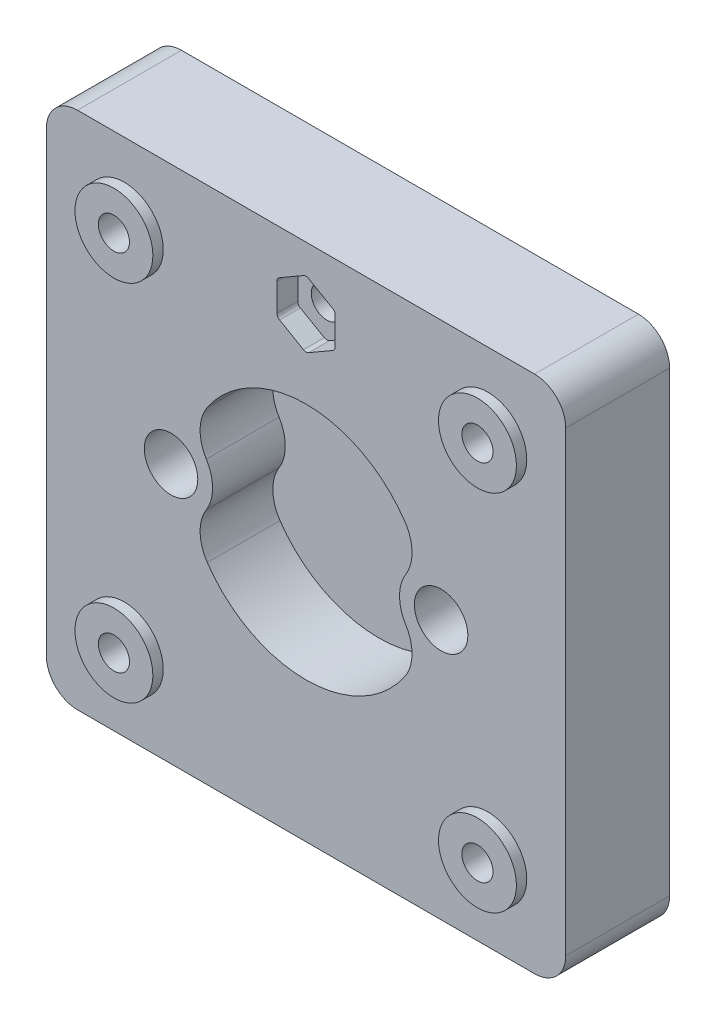
SolidWorks part; units mm, degrees
other "Cathode"
ref_plane "Front Plane" through (0, 0, 0) normal (0, 0, 1) x (1, 0, 0)
ref_plane "Top Plane" through (0, 0, 0) normal (0, 1, 0) x (1, 0, 0)
ref_plane "Right Plane" through (0, 0, 0) normal (1, 0, 0) x (0, 0, -1)
sketch "Sketch1" plane through (0, 0, 0) normal (0, 1, 0) x (1, 0, 0)
  line L1 (25, -25) -> (-25, -25)
  line L2 (25, -25) -> (25, 25)
  line L3 (25, 25) -> (-25, 25)
  line L4 (-25, -25) -> (-25, 25)
  line L5 (25, -25) -> (-25, 25) construction
  line L6 (25, 25) -> (-25, -25) construction
  point P0 (0, 0)
  dimension "D1" = 50
  dimension "D2" = 50
extrude "Body" add sketch "Sketch1" along normal blind 10
sketch "Sketch2" plane through (0, 10, 0) normal (0, 1, 0) x (1, 0, 0)
  circle A0 centre (0, 0) radius 11.5
  dimension "D1" = 23
extrude "Cut view" cut sketch "Sketch2" against normal blind 7
fillet "FilletBody" radius 3 4 edges at (-25, 5, -25) (25, 5, -25) (25, 5, 25) (-25, 5, 25)
sketch "Sketch3" plane through (0, 10, 0) normal (0, 1, 0) x (1, 0, 0)
  line L0 (-25, 22) -> (-25, -22) construction
  line L1 (22, 25) -> (-22, 25) construction
  line L2 (-38.934, 0) -> (38.0552, 0) construction
  line L3 (0, 29.5616) -> (0, -31.3312) construction
  circle A0 centre (-17.5, 17.5) radius 3.75
  circle A1 centre (17.5, 17.5) radius 3.75
  circle A2 centre (17.5, -17.5) radius 3.75
  circle A3 centre (-17.5, -17.5) radius 3.75
  dimension "D1" = 7.5
  dimension "D2" = 7.5
  dimension "D3" = 7.5
extrude "Bolt extrude" add sketch "Sketch3" along normal blind 1
sketch "Sketch4" plane through (0, 11, 0) normal (0, 1, 0) x (1, 0, 0)
  line L2 (-40.7589, 0) -> (37.9331, 0) construction
  line L3 (-5.5, 0) -> (5.5, 0) construction
  line L4 (0, 29.2624) -> (0, -30.4072) construction
  circle A0 centre (-17.5, 17.5) radius 1.5
  circle A1 centre (17.5, 17.5) radius 1.5
  circle A2 centre (17.5, -17.5) radius 1.5
  circle A3 centre (-17.5, -17.5) radius 1.5
  dimension "D1" = 3
extrude "Bolt" cut sketch "Sketch4" against normal blind 16 and the other way blind 10
sketch "Sketch5" plane through (0, 10, 0) normal (0, 1, 0) x (1, 0, 0)
  line L0 (22, 25) -> (-22, 25) construction
  line L1 (0, 22.2332) -> (-2.8, 20.6166)
  line L2 (-2.8, 20.6166) -> (-2.8, 17.3834)
  line L3 (-2.8, 17.3834) -> (0, 15.7668)
  line L4 (0, 15.7668) -> (2.8, 17.3834)
  line L5 (2.8, 17.3834) -> (2.8, 20.6166)
  line L6 (2.8, 20.6166) -> (0, 22.2332)
  circle A0 centre (0, 19) radius 2.8 construction
  dimension "D2" = 5.6
  dimension "D1" = 6
extrude "Hex" cut sketch "Sketch5" against normal blind 2
sketch "Sketch19" plane through (0, 8, 0) normal (0, 1, 0) x (1, 0, 0)
  circle A0 centre (0, 19) radius 1.5
  dimension "D1" = 3
extrude "Hex_bolt" cut sketch "Sketch19" against normal blind 3
sketch "Sketch6" plane through (0, 10, 0) normal (0, 1, 0) x (1, 0, 0)
  line L0 (-5.5, 0) -> (5.5, 0) construction
  line L1 (-25, 22) -> (-25, -22) construction
  line L2 (0, 27.3129) -> (0, -30.0369) construction
  circle A0 centre (-13, 0) radius 4
  circle A1 centre (13, 0) radius 4
  dimension "D2" = 8
  dimension "D1" = 12
extrude "Field1" add sketch "Sketch6" against normal blind 7
fillet "Field2" radius 4 4 edges at (10.9712, 6.5, -3.4473) (10.9712, 6.5, 3.4473) (-10.9712, 6.5, 3.4473) (-10.9712, 6.5, -3.4473)
sketch "Sketch7" plane through (0, 10, 0) normal (0, 1, 0) x (1, 0, 0)
  line L0 (-5.5, 0) -> (5.5, 0) construction
  line L1 (-25, 22) -> (-25, -22) construction
  line L2 (0, 27.9755) -> (0, -30.6258) construction
  circle A0 centre (-13, 0) radius 2.575
  circle A1 centre (13, 0) radius 2.575
  dimension "D2" = 5.15
  dimension "D1" = 12
extrude "Ports1" add sketch "Sketch7" along normal blind 12
sketch "Sketch10" plane through (0, 22, 0) normal (0, 1, 0) x (1, 0, 0)
  line L0 (0, 29.9579) -> (0, -31.6237) construction
  circle A0 centre (-13, 0) radius 1.575
  circle A1 centre (13, 0) radius 1.575
  dimension "D1" = 3.15
extrude "Ports2" cut sketch "Sketch10" against normal blind 32 and the other way blind 12
sketch "Sketch11" plane through (0, 0, 0) normal (0, -1, 0) x (1, 0, 0)
  circle A0 centre (0, 0) radius 15
  circle A1 centre (0, 0) radius 20
  dimension "D1" = 30
  dimension "D2" = 40
extrude "Seal1" cut sketch "Sketch11" against normal blind 0.5 contours A1 A0
sketch "Sketch15" plane through (0, 0, 0) normal (0, -1, 0) x (1, 0, 0)
  line L0 (5.5, 0) -> (-5.5, 0) construction
  line L1 (-14, 0) -> (-12, 0)
  line L2 (-8, 0) -> (-6, 0)
  line L3 (3, 0) -> (5, 0)
  line L4 (9, 0) -> (11, 0)
  line L5 (-31.4935, 0) -> (32.7979, 0) construction
  arc A0 (-14, 0) -> (13.523, 3.6235) centre (0, 0) cw
  arc A1 (-8, 0) -> (7.2505, 3.3809) centre (0, 0) cw
  arc A2 (-12, 0) -> (11.5911, 3.1058) centre (0, 0) cw
  arc A3 (-6, 0) -> (5.4378, 2.5357) centre (0, 0) cw
  arc A4 (13.523, 3.6235) -> (11.5911, 3.1058) centre (12.557, 3.3646) cw
  arc A5 (7.2505, 3.3809) -> (5.4378, 2.5357) centre (6.3442, 2.9583) cw
  arc A6 (11, 0) -> (-10.3366, 3.7622) centre (0, 0) ccw
  arc A7 (9, 0) -> (-8.4572, 3.0782) centre (0, 0) ccw
  arc A8 (5, 0) -> (-3.5355, 3.5355) centre (0, 0) ccw
  arc A9 (3, 0) -> (-2.1213, 2.1213) centre (0, 0) ccw
  arc A10 (-10.3366, 3.7622) -> (-8.4572, 3.0782) centre (-9.3969, 3.4202) ccw
  arc A11 (-3.5355, 3.5355) -> (-2.1213, 2.1213) centre (-2.8284, 2.8284) ccw
  arc A12 (3, 0) -> (-2.1213, -2.1213) centre (0, 0) cw
  arc A13 (-3.5355, -3.5355) -> (-2.1213, -2.1213) centre (-2.8284, -2.8284) cw
  arc A14 (5, 0) -> (-3.5355, -3.5355) centre (0, 0) cw
  arc A15 (-8, 0) -> (7.2505, -3.3809) centre (0, 0) ccw
  arc A16 (-6, 0) -> (5.4378, -2.5357) centre (0, 0) ccw
  arc A17 (7.2505, -3.3809) -> (5.4378, -2.5357) centre (6.3442, -2.9583) ccw
  arc A18 (9, 0) -> (-8.4572, -3.0782) centre (0, 0) cw
  arc A19 (-10.3366, -3.7622) -> (-8.4572, -3.0782) centre (-9.3969, -3.4202) cw
  arc A20 (11, 0) -> (-10.3366, -3.7622) centre (0, 0) cw
  arc A21 (-14, 0) -> (13.523, -3.6235) centre (0, 0) ccw
  arc A22 (-12, 0) -> (11.5911, -3.1058) centre (0, 0) ccw
  arc A23 (13.523, -3.6235) -> (11.5911, -3.1058) centre (12.557, -3.3646) ccw
  circle M18 centre (-13, 0) radius 1.575
  dimension "D1" = 165
  dimension "D2" = 155
  dimension "D5" = 14
  dimension "D6" = 8
  dimension "D7" = 160
  dimension "D8" = 11
  dimension "D10" = 5
  dimension "D11" = 135
  dimension "D3" = 2
  dimension "D4" = 2
  dimension "D9" = 2
  dimension "D12" = 2
extrude "FlowField" cut sketch "Sketch15" against normal blind 1.5 contours A4 A0 A2 M18 | A6 A10 A7 L4 | A5 A1 L2 A3 | A8 A11 A9 L3 | A14 L3 A12 A13 | A15 A17 A16 L2 | A20 L4 A18 A19 | A21 A23 A22 M18
sketch "Sketch16" plane through (0, 0, 0) normal (0, -1, 0) x (1, 0, 0)
  line L0 (-13, 0) -> (0, 0) construction
  line L1 (-13, 1) -> (0, 1)
  line L2 (-13, -1) -> (0, -1)
  line L3 (13, 0) -> (4.4291, 0) construction
  line L4 (5.5, 0) -> (-5.5, 0) construction
  line L5 (13, -1) -> (4.4291, -1)
  line L6 (13, 1) -> (4.4291, 1)
  arc A0 (-13, 1) -> (-13, -1) centre (-13, 0) ccw
  arc A1 (0, -1) -> (0, 1) centre (0, 0) ccw
  arc A2 (13, -1) -> (13, 1) centre (13, 0) ccw
  arc A3 (4.4291, 1) -> (4.4291, -1) centre (4.4291, 0) ccw
  point P4 (-6.5, 0)
  point P14 (8.7146, 0)
  dimension "D1" = 1
  dimension "D2" = 1
extrude "FlowField_Channel" cut sketch "Sketch16" against normal blind 1.5
move or copy body "Body-Move/Copy1" bodies to move or copy 112 copy no rotation origin (0, 11, 0) rotation axis (1, 0, 0) rotation angle 90
sketch "Sketch20" plane through (0, 0, 11) normal (0, 0, 1) x (1, 0, 0)
  circle A0 centre (-13, 11) radius 2.575 construction
  circle A1 centre (13, 11) radius 2.575
  circle A2 centre (13, 11) radius 2.575
  circle A3 centre (-13, 11) radius 2.575
  dimension "D1" = 0
extrude "Cut-Extrude1" cut sketch "Sketch20" against normal blind 17
fillet "Fillet1" radius 0.5 6 edges at (2.8, 28.3834, -2) (0, 26.7668, -2) (-2.8, 28.3834, -2) (-2.8, 31.6166, -2) (2.8, 31.6166, -2) (0, 33.2332, -2)
